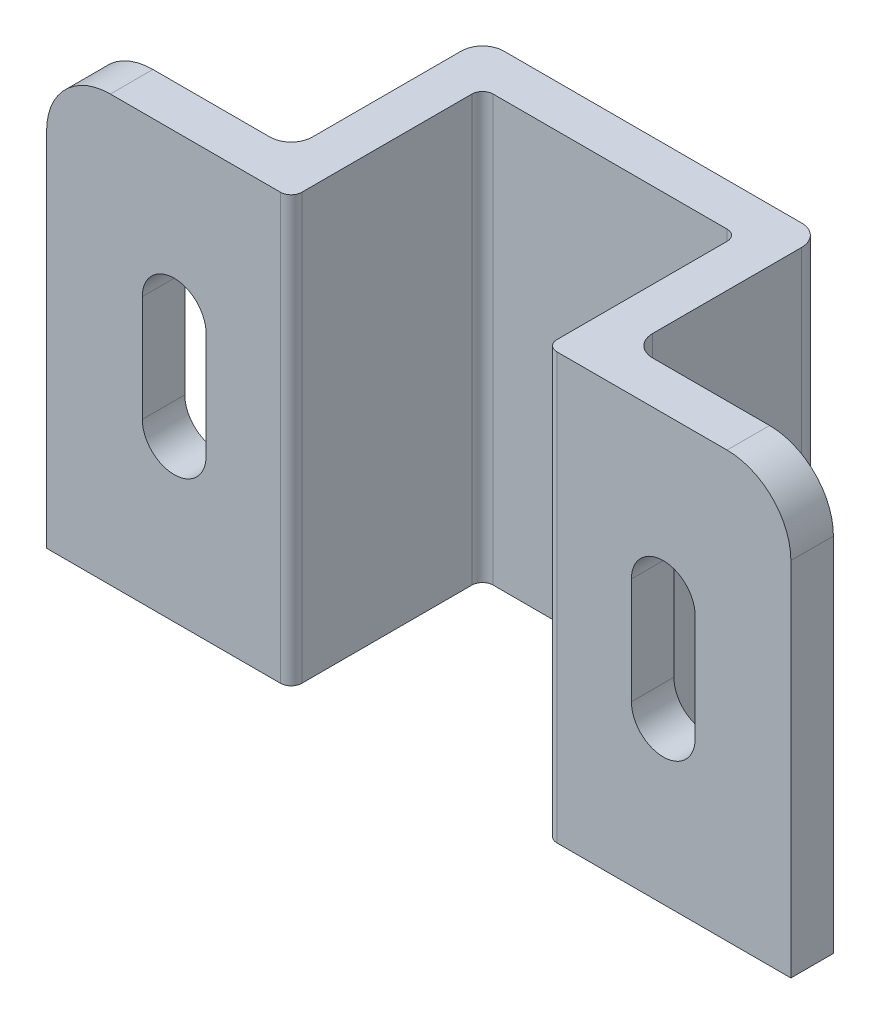
SolidWorks part; units mm, degrees
ref_plane "Front Plane" through (0, 0, 0) normal (0, 0, 1) x (1, 0, 0)
ref_plane "Top Plane" through (0, 0, 0) normal (0, 1, 0) x (1, 0, 0)
ref_plane "Right Plane" through (0, 0, 0) normal (1, 0, 0) x (0, 0, -1)
sketch "Sketch1" plane through (0, 0, 0) normal (0, 0, 1) x (1, 0, 0)
  line L1 (0, 0) -> (35, 0)
  line L2 (0, 0) -> (0, 20)
  line L3 (0, 20) -> (35, 20)
  line L4 (35, 0) -> (35, 20)
  dimension "D1" = 35
  dimension "D2" = 20
extrude "Boss-Extrude1" add sketch "Sketch1" along normal blind 2
sketch "Sketch4" plane through (0, 0, 2) normal (0, 0, 1) x (1, 0, 0)
  line L0 (17.5, 20) -> (17.5, 0) construction
  line L1 (35, 20) -> (0, 20) construction
  line L2 (0, 0) -> (35, 0) construction
  line L3 (11.5, 10) -> (23.5, 10) construction
  line L5 (0, 20) -> (11.5, 20)
  line L6 (0, 20) -> (0, 0)
  line L7 (0, 0) -> (11.5, 0)
  line L8 (11.5, 20) -> (11.5, 0)
  line L9 (35, 20) -> (23.5, 20)
  line L10 (35, 20) -> (35, 0)
  line L11 (35, 0) -> (23.5, 0)
  line L12 (23.5, 20) -> (23.5, 0)
  point P8 (17.5, 10)
  point P9 (17.5, 10)
  dimension "D1" = 12
extrude "Boss-Extrude2" add sketch "Sketch4" along normal blind 9
sketch "Sketch5" plane through (0, 20, 0) normal (0, 1, 0) x (1, 0, 0)
  line L0 (11.5, -11) -> (11.5, -2) construction
  line L1 (0, 0) -> (9.5, 0)
  line L2 (0, 0) -> (0, -9)
  line L3 (0, -9) -> (9.5, -9)
  line L4 (9.5, 0) -> (9.5, -9)
  line L5 (35, 0) -> (25.5, 0)
  line L6 (35, 0) -> (35, -9)
  line L7 (35, -9) -> (25.5, -9)
  line L8 (25.5, 0) -> (25.5, -9)
  line L9 (23.5, -11) -> (23.5, -2) construction
  line L10 (11.5, -11) -> (0, -11) construction
  line L11 (35, -11) -> (23.5, -11) construction
  dimension "D1" = 2
  dimension "D2" = 2
  dimension "D3" = 2
  dimension "D4" = 2
extrude "Cut-Extrude2" cut sketch "Sketch5" against normal through all
fillet "Fillet1" radius 1 4 edges at (25.5, 10, 9) (9.5, 10, 9) (25.5, 10, 0) (9.5, 10, 0)
fillet "Fillet2" radius 0.5 4 edges at (11.5, 10, 2) (23.5, 10, 2) (23.5, 10, 11) (11.5, 10, 11)
sketch "Sketch2" plane through (0, 0, 11) normal (0, 0, 1) x (1, 0, 0)
  line L0 (6, 10) -> (29, 10) construction
  line L3 (17.5, 20) -> (17.5, 0) construction
  line L5 (12, 0) -> (23, 0) construction
  line L6 (6, 12.5) -> (6, 7.5) construction
  line L7 (7.5, 12.5) -> (7.5, 7.5)
  line L8 (4.5, 12.5) -> (4.5, 7.5)
  line L9 (29, 12.5) -> (29, 7.5) construction
  line L10 (30.5, 12.5) -> (30.5, 7.5)
  line L11 (27.5, 12.5) -> (27.5, 7.5)
  line L18 (24.5, 20) -> (10.5, 20) construction
  arc A0 (7.5, 12.5) -> (4.5, 12.5) centre (6, 12.5) ccw
  arc A1 (4.5, 7.5) -> (7.5, 7.5) centre (6, 7.5) ccw
  arc A2 (30.5, 12.5) -> (27.5, 12.5) centre (29, 12.5) ccw
  arc A3 (27.5, 7.5) -> (30.5, 7.5) centre (29, 7.5) ccw
  point P2 (17.5, 10)
  point P12 (6, 10)
  point P18 (29, 10)
  point P45 (17.5, 10)
  dimension "D4" = 1.5
  dimension "D5" = 1.5
  dimension "D1" = 23
  dimension "D2" = 5
  dimension "D3" = 5
extrude "Cut-Extrude3" cut sketch "Sketch2" against normal through all
fillet "Fillet3" radius 3 2 edges at (0, 20, 10) (35, 20, 10)
